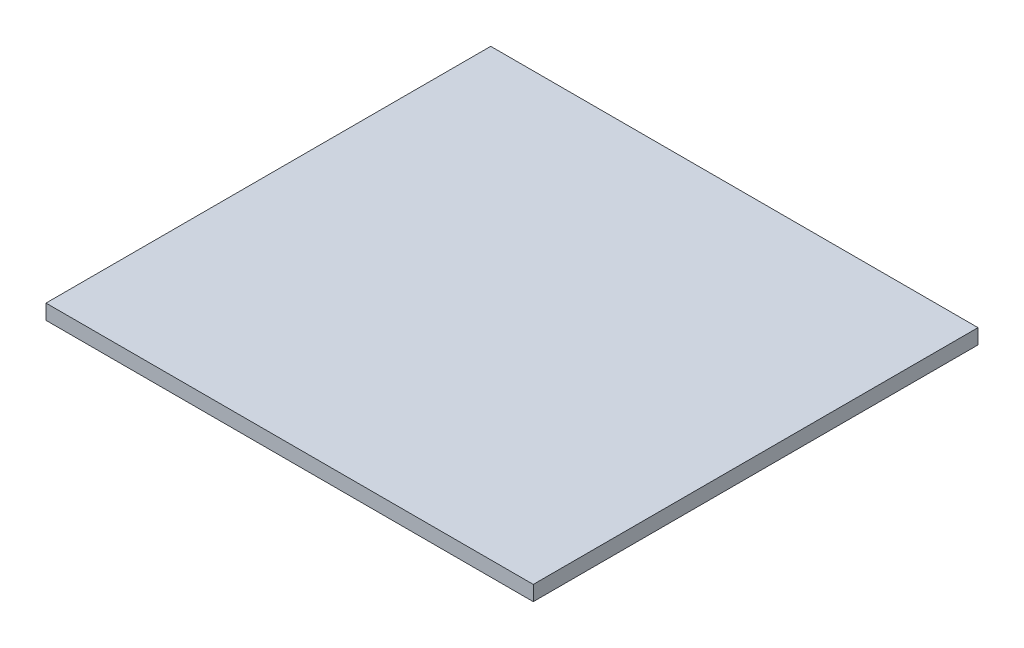
SolidWorks part; units mm, degrees
ref_plane "Front Plane" through (0, 0, 0) normal (0, 0, 1) x (1, 0, 0)
ref_plane "Top Plane" through (0, 0, 0) normal (0, 1, 0) x (1, 0, 0)
ref_plane "Right Plane" through (0, 0, 0) normal (1, 0, 0) x (0, 0, -1)
sketch "Sketch1" plane through (0, 0, 0) normal (0, 1, 0) x (1, 0, 0)
  line L1 (0, 0) -> (206.502, 0)
  line L2 (0, 0) -> (0, 188.468)
  line L3 (0, 188.468) -> (206.502, 188.468)
  line L4 (206.502, 0) -> (206.502, 188.468)
  dimension "D1" = 206.502
  dimension "D2" = 188.468
extrude "Boss-Extrude1" add sketch "Sketch1" along normal blind 6.35
